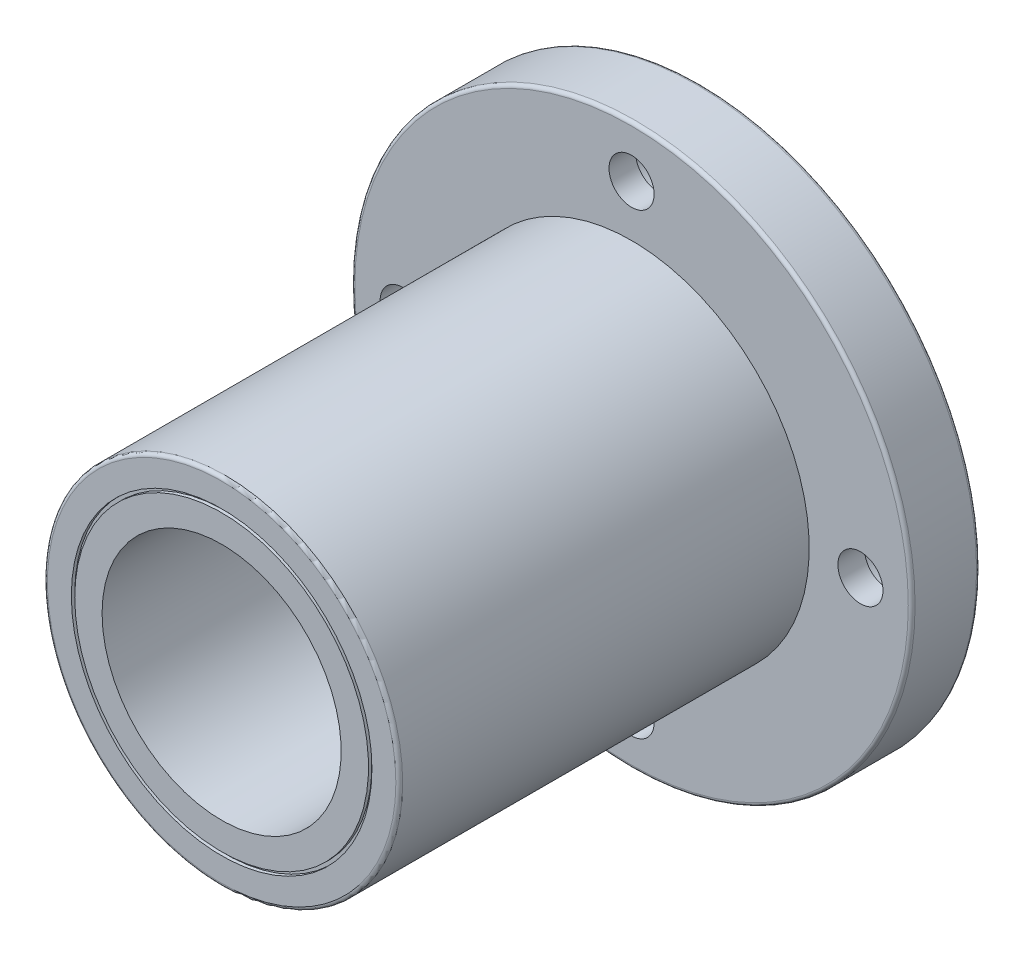
SolidWorks part; units mm, degrees
material "AISI 316 Отожженная нержавеющая сталь. полоса (SS)"
ref_plane "Plano frontal" through (0, 0, 0) normal (0, 0, 1) x (1, 0, 0)
ref_plane "Plano superior" through (0, 0, 0) normal (0, 1, 0) x (1, 0, 0)
ref_plane "Plano direito" through (0, 0, 0) normal (1, 0, 0) x (0, 0, -1)
sketch "Esboço1" plane through (0, 0, 0) normal (1, 0, 0) x (0, 0, -1)
  line L0 (0, 17.5) -> (0, 21.5)
  line L1 (0, 41) -> (-10, 41)
  line L2 (-10, 41) -> (-10, 26)
  line L3 (-10, 26) -> (-70, 26)
  line L4 (-70, 26) -> (-70, 22)
  line L5 (-70, 17.5) -> (0, 17.5)
  line L6 (0, 0) -> (-226.2321, 0) construction
  line L7 (-70, 22) -> (-69.5, 22)
  line L8 (-69.5, 22) -> (-69.5, 21.5)
  line L9 (-69.5, 21.5) -> (-70, 21.5)
  line L10 (0, 26) -> (-0.5, 26)
  line L11 (-0.5, 26) -> (-0.5, 25.5)
  line L12 (-0.5, 25.5) -> (0, 25.5)
  line L13 (0, 26) -> (0, 41)
  line L14 (-70, 21.5) -> (-70, 17.5)
  line L15 (0, 22) -> (-0.5, 22)
  line L16 (-0.5, 22) -> (-0.5, 21.5)
  line L17 (-0.5, 21.5) -> (0, 21.5)
  line L18 (0, 22) -> (0, 25.5)
  dimension "D1" = 70
  dimension "D2" = 52
  dimension "D3" = 35
  dimension "D4" = 82
  dimension "D5" = 10
  dimension "D6" = 0.5
  dimension "D7" = 0.5
  dimension "D8" = 0.5
  dimension "D9" = 0.5
  dimension "D10" = 0.5
  dimension "D11" = 0.5
revolve "Revolução1" add sketch "Esboço1" angle 360 about L6
sketch "Esboço5" plane through (0, 0, 0) normal (1, 0, 0) x (0, 0, -1)
  line L0 (0, 39) -> (-6.1, 39)
  line L1 (0, -41) -> (0, 41) construction
  line L2 (-6.1, 39) -> (-6.1, 36.8)
  line L3 (-6.1, 36.8) -> (-10, 36.8)
  line L4 (-10, 41) -> (-10, -41) construction
  line L5 (-10, 36.8) -> (-10, 33.5)
  line L6 (-10, 33.5) -> (0, 33.5)
  line L7 (0, 33.5) -> (0, 39)
  line L8 (0, 33.5) -> (2.2336, 33.5) construction
  line L9 (0, 0) -> (9.7959, 0) construction
  dimension "D1" = 11
  dimension "D2" = 6.6
  dimension "D3" = 6.1
  dimension "D4" = 67
revolve "Corte-Revolução1" cut sketch "Esboço5" angle 360 about L8
pattern_circular "PadrãoCircular1" count 4 over 360 about axis through (0, 0, 0) along (0, 0, 1) of "Corte-Revolução1"
fillet "Filete1" radius 0.5 3 edges at (-41, 0, 0) (-41, 0, 10) (-26, 0, 70)
